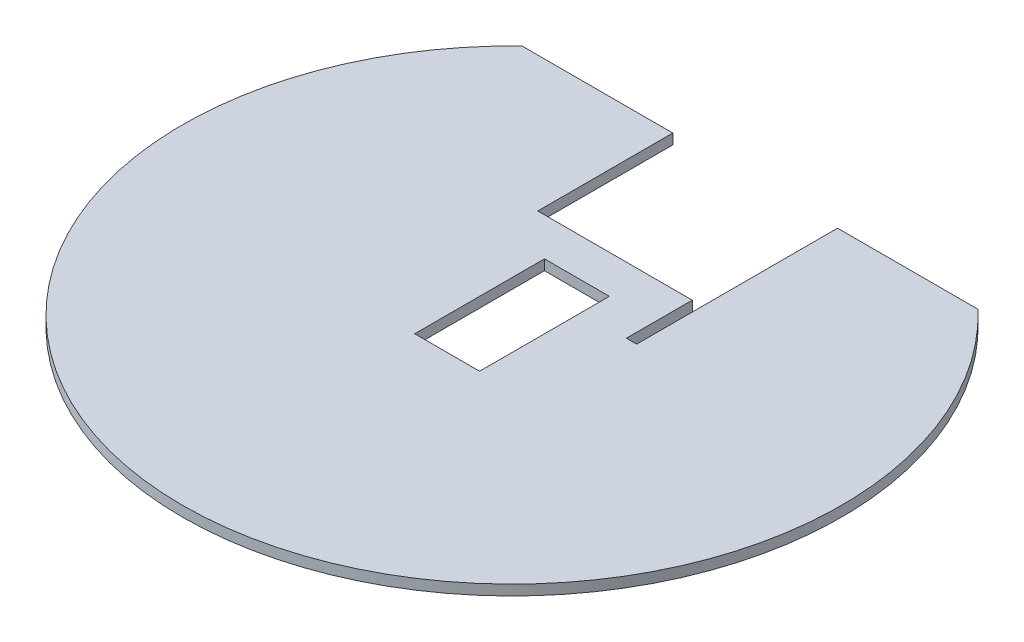
SolidWorks part; units mm, degrees
ref_plane "Front Plane" through (0, 0, 0) normal (0, 0, 1) x (1, 0, 0)
ref_plane "Top Plane" through (0, 0, 0) normal (0, 1, 0) x (1, 0, 0)
ref_plane "Right Plane" through (0, 0, 0) normal (1, 0, 0) x (0, 0, -1)
sketch "Sketch1" plane through (0, 0, 0) normal (0, 1, 0) x (1, 0, 0)
  line L0 (0, 101.6) -> (0, 31.75) construction
  line L1 (117.3176, 0) -> (58.6588, 101.6) construction
  line L2 (58.6588, 101.6) -> (-58.6588, 101.6) construction
  line L3 (-58.6588, 101.6) -> (-117.3176, 0) construction
  line L4 (-117.3176, 0) -> (-58.6588, -101.6) construction
  line L5 (-58.6588, -101.6) -> (58.6588, -101.6) construction
  line L6 (58.6588, -101.6) -> (117.3176, 0) construction
  line L7 (-23.8125, 31.75) -> (23.8125, 31.75)
  line L8 (23.8125, 31.75) -> (23.8125, 101.6)
  line L9 (-23.8125, 31.75) -> (-23.8125, 101.6)
  line L10 (-23.8125, 101.6) -> (23.8125, 101.6)
  circle A0 centre (0, 0) radius 101.6
  point P1 (0, 101.6)
  point P15 (0, 31.75)
  dimension "D1" = 101.6
  dimension "D2" = 47.625
  dimension "D3" = 69.85
extrude "Boss-Extrude1" add sketch "Sketch1" along normal blind 3.175 contours L7 L9 L2 L3 L4 L5 L6 L1 L8
sketch "Sketch2" plane through (0, 3.175, 0) normal (0, 1, 0) x (1, 0, 0)
  line L0 (23.8125, 31.75) -> (23.8125, 98.7701) construction
  line L1 (-10, -20) -> (10, -20)
  line L2 (-10, -20) -> (-10, 20)
  line L3 (-10, 20) -> (10, 20)
  line L4 (10, -20) -> (10, 20)
  line L5 (-10, -20) -> (10, 20) construction
  line L6 (-10, 20) -> (10, -20) construction
  line L7 (23.8125, 101.6) -> (26.9875, 101.6)
  line L8 (23.8125, 101.6) -> (23.8125, 11.43)
  line L9 (23.8125, 11.43) -> (26.9875, 11.43)
  line L10 (26.9875, 101.6) -> (26.9875, 11.43)
  line L11 (-23.8125, 31.75) -> (23.8125, 31.75) construction
  point P18 (0, 0)
  dimension "D1" = 3.175
  dimension "D2" = 40
  dimension "D3" = 20
  dimension "D4" = 20.32
extrude "Cut-Extrude1" cut sketch "Sketch2" against normal through all
sketch "Sketch3" plane through (0, 3.175, 0) normal (0, 1, 0) x (1, 0, 0)
  line L1 (-70.2808, 73.3701) -> (70.2808, 73.3701)
  line L2 (-70.2808, 73.3701) -> (-70.2808, 98.7701)
  line L3 (-70.2808, 98.7701) -> (70.2808, 98.7701)
  line L4 (70.2808, 73.3701) -> (70.2808, 98.7701)
  arc A0 (-23.8125, 98.7701) -> (26.9875, 97.9502) centre (0, 0) ccw construction
  point P4 (0, 0)
  point P8 (0, 0)
  point P9 (0, 0)
  dimension "D1" = 25.4
extrude "Cut-Extrude2" cut sketch "Sketch3" against normal through all
